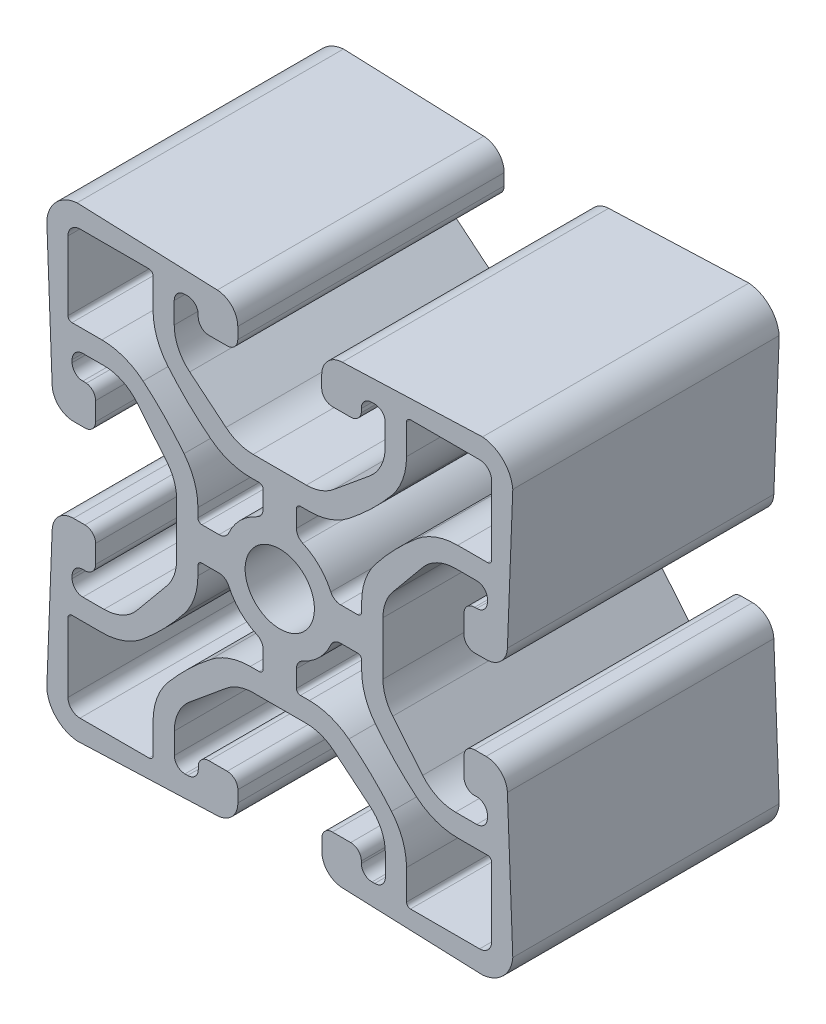
SolidWorks part; units mm, degrees
material "6061 Alloy"
ref_plane "Front" through (0, 0, 0) normal (0, 0, 1) x (1, 0, 0)
ref_plane "Top" through (0, 0, 0) normal (0, 1, 0) x (1, 0, 0)
ref_plane "Right" through (0, 0, 0) normal (1, 0, 0) x (0, 0, -1)
sketch "Sketch1" plane through (0, 0, 0) normal (0, 0, 1) x (1, 0, 0)
  line L0 (19.3255, 22.213) -> (5.9504, 21.6992)
  line L1 (22.2128, 19.328) -> (21.6992, 5.9586)
  line L2 (3.9964, 18.5751) -> (3.9964, 19.6687)
  line L3 (18.5751, 4.0046) -> (19.6687, 4.0046)
  line L4 (5.0124, 17.5591) -> (6.7625, 17.5591)
  line L5 (17.5591, 6.7605) -> (17.5591, 5.0206)
  line L6 (7.7683, 18.4316) -> (7.7683, 18.4431)
  line L7 (18.7783, 7.7765) -> (18.5751, 7.7765)
  line L8 (7.7683, 18.4431) -> (7.7683, 18.7783)
  line L9 (19.7943, 9.0465) -> (19.7943, 8.7925)
  line L10 (8.7843, 19.7943) -> (9.0383, 19.7943)
  line L11 (18.7783, 10.0625) -> (16.7556, 10.0625)
  line L12 (10.0543, 18.7783) -> (10.0543, 16.7556)
  line L13 (13.6222, 8.5866) -> (10.7682, 5.1313)
  line L14 (8.5785, 13.6222) -> (5.1232, 10.7682)
  line L15 (9.8375, 0.0041) -> (9.8375, 2.5432)
  line L16 (-0.0041, 9.8375) -> (2.5351, 9.8375)
  line L17 (9.8375, 0.0041) -> (9.8375, -2.5351)
  line L18 (-0.0041, 9.8375) -> (-2.5432, 9.8375)
  line L19 (13.6222, -8.5785) -> (10.7682, -5.1232)
  line L20 (-8.5866, 13.6222) -> (-5.1313, 10.7682)
  line L21 (18.7783, -10.0543) -> (16.7556, -10.0543)
  line L22 (-10.0625, 18.7783) -> (-10.0625, 16.7556)
  line L23 (19.7943, -8.7843) -> (19.7943, -9.0383)
  line L24 (-9.0465, 19.7943) -> (-8.7925, 19.7943)
  line L25 (18.4431, -7.7683) -> (18.7783, -7.7683)
  line L26 (-7.7765, 18.7783) -> (-7.7765, 18.5751)
  line L27 (18.4316, -7.7683) -> (18.4431, -7.7683)
  line L28 (-6.7605, 17.5591) -> (-5.0206, 17.5591)
  line L29 (17.5591, -5.0124) -> (17.5591, -6.7625)
  line L30 (-4.0046, 18.5751) -> (-4.0046, 19.6687)
  line L31 (18.5751, -3.9964) -> (19.6687, -3.9964)
  line L32 (-19.328, 22.2128) -> (-5.9586, 21.6992)
  line L33 (22.213, -19.3255) -> (21.6992, -5.9504)
  line L34 (-22.213, 19.3255) -> (-21.6992, 5.9504)
  line L35 (19.328, -22.2128) -> (5.9586, -21.6992)
  line L36 (-18.5751, 3.9964) -> (-19.6687, 3.9964)
  line L37 (4.0046, -18.5751) -> (4.0046, -19.6687)
  line L38 (-17.5591, 5.0124) -> (-17.5591, 6.7625)
  line L39 (6.7605, -17.5591) -> (5.0206, -17.5591)
  line L40 (-18.4316, 7.7683) -> (-18.4431, 7.7683)
  line L41 (7.7765, -18.7783) -> (7.7765, -18.5751)
  line L42 (-18.4431, 7.7683) -> (-18.7783, 7.7683)
  line L43 (9.0465, -19.7943) -> (8.7925, -19.7943)
  line L44 (-19.7943, 8.7843) -> (-19.7943, 9.0383)
  line L45 (10.0625, -18.7783) -> (10.0625, -16.7556)
  line L46 (-18.7783, 10.0543) -> (-16.7556, 10.0543)
  line L47 (8.5866, -13.6222) -> (5.1313, -10.7682)
  line L48 (-13.6222, 8.5785) -> (-10.7682, 5.1232)
  line L49 (0.0041, -9.8375) -> (2.5432, -9.8375)
  line L50 (-9.8375, -0.0041) -> (-9.8375, 2.5351)
  line L51 (0.0041, -9.8375) -> (-2.5351, -9.8375)
  line L52 (-9.8375, -0.0041) -> (-9.8375, -2.5432)
  line L53 (-8.5785, -13.6222) -> (-5.1232, -10.7682)
  line L54 (-13.6222, -8.5866) -> (-10.7682, -5.1313)
  line L55 (-10.0543, -18.7783) -> (-10.0543, -16.7556)
  line L56 (-18.7783, -10.0625) -> (-16.7556, -10.0625)
  line L57 (-8.7843, -19.7943) -> (-9.0383, -19.7943)
  line L58 (-19.7943, -9.0465) -> (-19.7943, -8.7925)
  line L59 (-7.7683, -18.4431) -> (-7.7683, -18.7783)
  line L60 (-18.7783, -7.7765) -> (-18.5751, -7.7765)
  line L61 (-7.7683, -18.4316) -> (-7.7683, -18.4431)
  line L62 (-17.5591, -6.7605) -> (-17.5591, -5.0206)
  line L63 (-5.0124, -17.5591) -> (-6.7625, -17.5591)
  line L64 (-18.5751, -4.0046) -> (-19.6687, -4.0046)
  line L65 (-3.9964, -18.5751) -> (-3.9964, -19.6687)
  line L66 (-22.2128, -19.328) -> (-21.6992, -5.9586)
  line L67 (-19.3255, -22.213) -> (-5.9504, -21.6992)
  line L68 (-1.5875, -7.4245) -> (-1.5875, -5.7917)
  line L69 (-1.9685, -7.8055) -> (-2.8117, -7.8055)
  line L70 (-5.7917, -1.5875) -> (-7.4245, -1.5875)
  line L71 (-12.0821, -16.9617) -> (-12.0821, -19.812)
  line L72 (-7.8055, -2.8198) -> (-7.8055, -1.9685)
  line L73 (-12.4631, -20.193) -> (-19.05, -20.193)
  line L74 (-20.193, -19.05) -> (-20.193, -12.4631)
  line L75 (-19.812, -12.0821) -> (-16.9617, -12.0821)
  line L76 (-7.4245, 1.5875) -> (-5.7917, 1.5875)
  line L77 (-7.8055, 1.9685) -> (-7.8055, 2.8117)
  line L78 (-1.5875, 5.7917) -> (-1.5875, 7.4245)
  line L79 (-16.9617, 12.0821) -> (-19.812, 12.0821)
  line L80 (-2.8198, 7.8055) -> (-1.9685, 7.8055)
  line L81 (-20.193, 12.4631) -> (-20.193, 19.05)
  line L82 (-19.05, 20.193) -> (-12.4631, 20.193)
  line L83 (-12.0821, 19.812) -> (-12.0821, 16.9617)
  line L84 (7.4245, -1.5875) -> (5.7917, -1.5875)
  line L85 (7.8055, -1.9685) -> (7.8055, -2.8117)
  line L86 (1.5875, -5.7917) -> (1.5875, -7.4245)
  line L87 (16.9617, -12.0821) -> (19.812, -12.0821)
  line L88 (2.8198, -7.8055) -> (1.9685, -7.8055)
  line L89 (20.193, -12.4631) -> (20.193, -19.05)
  line L90 (19.05, -20.193) -> (12.4631, -20.193)
  line L91 (12.0821, -19.812) -> (12.0821, -16.9617)
  line L92 (7.8055, 2.8198) -> (7.8055, 1.9685)
  line L93 (5.7917, 1.5875) -> (7.4245, 1.5875)
  line L94 (19.812, 12.0821) -> (16.9617, 12.0821)
  line L95 (1.5875, 7.4245) -> (1.5875, 5.7917)
  line L96 (20.193, 19.05) -> (20.193, 12.4631)
  line L97 (1.9685, 7.8055) -> (2.8117, 7.8055)
  line L98 (12.4631, 20.193) -> (19.05, 20.193)
  line L99 (12.0821, 16.9617) -> (12.0821, 19.812)
  circle A0 centre (0, 0) radius 3.302
  arc A1 (22.2128, 19.328) -> (19.3255, 22.213) centre (19.05, 19.05) ccw
  arc A2 (5.9504, 21.6992) -> (3.9964, 19.6687) centre (6.0284, 19.6687) ccw
  arc A3 (19.6687, 4.0046) -> (21.6992, 5.9586) centre (19.6687, 6.0366) ccw
  arc A4 (3.9964, 18.5751) -> (5.0124, 17.5591) centre (5.0124, 18.5751) ccw
  arc A5 (17.5591, 5.0206) -> (18.5751, 4.0046) centre (18.5751, 5.0206) ccw
  arc A6 (6.7625, 17.5591) -> (7.7683, 18.4316) centre (6.7625, 18.5751) ccw
  arc A7 (18.5751, 7.7765) -> (17.5591, 6.7605) centre (18.5751, 6.7605) ccw
  arc A8 (18.7783, 7.7765) -> (19.7943, 8.7925) centre (18.7783, 8.7925) ccw
  arc A9 (8.7843, 19.7943) -> (7.7683, 18.7783) centre (8.7843, 18.7783) ccw
  arc A10 (19.7943, 9.0465) -> (18.7783, 10.0625) centre (18.7783, 9.0465) ccw
  arc A11 (10.0543, 18.7783) -> (9.0383, 19.7943) centre (9.0383, 18.7783) ccw
  arc A12 (16.7556, 10.0625) -> (13.6222, 8.5866) centre (16.7556, 5.9985) ccw
  arc A13 (8.5785, 13.6222) -> (10.0543, 16.7556) centre (5.9903, 16.7556) ccw
  arc A14 (10.7682, 5.1313) -> (9.8375, 2.5432) centre (13.9015, 2.5432) ccw
  arc A15 (2.5351, 9.8375) -> (5.1232, 10.7682) centre (2.5351, 13.9015) ccw
  arc A16 (9.8375, -2.5351) -> (10.7682, -5.1232) centre (13.9015, -2.5351) ccw
  arc A17 (-5.1313, 10.7682) -> (-2.5432, 9.8375) centre (-2.5432, 13.9015) ccw
  arc A18 (13.6222, -8.5785) -> (16.7556, -10.0543) centre (16.7556, -5.9903) ccw
  arc A19 (-10.0625, 16.7556) -> (-8.5866, 13.6222) centre (-5.9985, 16.7556) ccw
  arc A20 (18.7783, -10.0543) -> (19.7943, -9.0383) centre (18.7783, -9.0383) ccw
  arc A21 (-9.0465, 19.7943) -> (-10.0625, 18.7783) centre (-9.0465, 18.7783) ccw
  arc A22 (19.7943, -8.7843) -> (18.7783, -7.7683) centre (18.7783, -8.7843) ccw
  arc A23 (-7.7765, 18.7783) -> (-8.7925, 19.7943) centre (-8.7925, 18.7783) ccw
  arc A24 (-7.7765, 18.5751) -> (-6.7605, 17.5591) centre (-6.7605, 18.5751) ccw
  arc A25 (17.5591, -6.7625) -> (18.4316, -7.7683) centre (18.5751, -6.7625) ccw
  arc A26 (-5.0206, 17.5591) -> (-4.0046, 18.5751) centre (-5.0206, 18.5751) ccw
  arc A27 (18.5751, -3.9964) -> (17.5591, -5.0124) centre (18.5751, -5.0124) ccw
  arc A28 (-4.0046, 19.6687) -> (-5.9586, 21.6992) centre (-6.0366, 19.6687) ccw
  arc A29 (21.6992, -5.9504) -> (19.6687, -3.9964) centre (19.6687, -6.0284) ccw
  arc A30 (-19.328, 22.2128) -> (-22.213, 19.3255) centre (-19.05, 19.05) ccw
  arc A31 (19.328, -22.2128) -> (22.213, -19.3255) centre (19.05, -19.05) ccw
  arc A32 (-21.6992, 5.9504) -> (-19.6687, 3.9964) centre (-19.6687, 6.0284) ccw
  arc A33 (4.0046, -19.6687) -> (5.9586, -21.6992) centre (6.0366, -19.6687) ccw
  arc A34 (-18.5751, 3.9964) -> (-17.5591, 5.0124) centre (-18.5751, 5.0124) ccw
  arc A35 (5.0206, -17.5591) -> (4.0046, -18.5751) centre (5.0206, -18.5751) ccw
  arc A36 (-17.5591, 6.7625) -> (-18.4316, 7.7683) centre (-18.5751, 6.7625) ccw
  arc A37 (7.7765, -18.5751) -> (6.7605, -17.5591) centre (6.7605, -18.5751) ccw
  arc A38 (7.7765, -18.7783) -> (8.7925, -19.7943) centre (8.7925, -18.7783) ccw
  arc A39 (-19.7943, 8.7843) -> (-18.7783, 7.7683) centre (-18.7783, 8.7843) ccw
  arc A40 (9.0465, -19.7943) -> (10.0625, -18.7783) centre (9.0465, -18.7783) ccw
  arc A41 (-18.7783, 10.0543) -> (-19.7943, 9.0383) centre (-18.7783, 9.0383) ccw
  arc A42 (10.0625, -16.7556) -> (8.5866, -13.6222) centre (5.9985, -16.7556) ccw
  arc A43 (-13.6222, 8.5785) -> (-16.7556, 10.0543) centre (-16.7556, 5.9903) ccw
  arc A44 (5.1313, -10.7682) -> (2.5432, -9.8375) centre (2.5432, -13.9015) ccw
  arc A45 (-9.8375, 2.5351) -> (-10.7682, 5.1232) centre (-13.9015, 2.5351) ccw
  arc A46 (-2.5351, -9.8375) -> (-5.1232, -10.7682) centre (-2.5351, -13.9015) ccw
  arc A47 (-10.7682, -5.1313) -> (-9.8375, -2.5432) centre (-13.9015, -2.5432) ccw
  arc A48 (-8.5785, -13.6222) -> (-10.0543, -16.7556) centre (-5.9903, -16.7556) ccw
  arc A49 (-16.7556, -10.0625) -> (-13.6222, -8.5866) centre (-16.7556, -5.9985) ccw
  arc A50 (-10.0543, -18.7783) -> (-9.0383, -19.7943) centre (-9.0383, -18.7783) ccw
  arc A51 (-19.7943, -9.0465) -> (-18.7783, -10.0625) centre (-18.7783, -9.0465) ccw
  arc A52 (-8.7843, -19.7943) -> (-7.7683, -18.7783) centre (-8.7843, -18.7783) ccw
  arc A53 (-18.7783, -7.7765) -> (-19.7943, -8.7925) centre (-18.7783, -8.7925) ccw
  arc A54 (-18.5751, -7.7765) -> (-17.5591, -6.7605) centre (-18.5751, -6.7605) ccw
  arc A55 (-6.7625, -17.5591) -> (-7.7683, -18.4316) centre (-6.7625, -18.5751) ccw
  arc A56 (-17.5591, -5.0206) -> (-18.5751, -4.0046) centre (-18.5751, -5.0206) ccw
  arc A57 (-3.9964, -18.5751) -> (-5.0124, -17.5591) centre (-5.0124, -18.5751) ccw
  arc A58 (-19.6687, -4.0046) -> (-21.6992, -5.9586) centre (-19.6687, -6.0366) ccw
  arc A59 (-5.9504, -21.6992) -> (-3.9964, -19.6687) centre (-6.0284, -19.6687) ccw
  arc A60 (-22.2128, -19.328) -> (-19.3255, -22.213) centre (-19.05, -19.05) ccw
  arc A61 (-1.9685, -7.8055) -> (-1.5875, -7.4245) centre (-1.9685, -7.4245) ccw
  arc A62 (-1.5875, -5.7917) -> (-2.1869, -4.8651) centre (-2.6035, -5.7917) ccw
  arc A63 (-2.8117, -7.8055) -> (-6.6038, -9.1286) centre (-2.8117, -13.9015) ccw
  arc A64 (-4.8651, -2.1869) -> (-2.1869, -4.8651) centre (0, 0) ccw
  arc A65 (-6.6038, -9.1286) -> (-10.6477, -13.0335) centre (10.3295, -30.7105) ccw
  arc A66 (-4.8651, -2.1869) -> (-5.7917, -1.5875) centre (-5.7917, -2.6035) ccw
  arc A67 (-10.6477, -13.0335) -> (-12.0821, -16.9617) centre (-5.9861, -16.9617) ccw
  arc A68 (-7.4245, -1.5875) -> (-7.8055, -1.9685) centre (-7.4245, -1.9685) ccw
  arc A69 (-12.4631, -20.193) -> (-12.0821, -19.812) centre (-12.4631, -19.812) ccw
  arc A70 (-9.1044, -6.5813) -> (-7.8055, -2.8198) centre (-13.9015, -2.8198) ccw
  arc A71 (-20.193, -19.05) -> (-19.05, -20.193) centre (-19.05, -19.05) ccw
  arc A72 (-13.039, -10.6523) -> (-9.1044, -6.5813) centre (-30.6913, 10.3456) ccw
  arc A73 (-16.9617, -12.0821) -> (-13.039, -10.6523) centre (-16.9617, -5.9861) ccw
  arc A74 (-19.812, -12.0821) -> (-20.193, -12.4631) centre (-19.812, -12.4631) ccw
  arc A75 (-7.8055, 1.9685) -> (-7.4245, 1.5875) centre (-7.4245, 1.9685) ccw
  arc A76 (-5.7917, 1.5875) -> (-4.8651, 2.1869) centre (-5.7917, 2.6035) ccw
  arc A77 (-7.8055, 2.8117) -> (-9.1286, 6.6038) centre (-13.9015, 2.8117) ccw
  arc A78 (-2.1869, 4.8651) -> (-4.8651, 2.1869) centre (0, 0) ccw
  arc A79 (-9.1286, 6.6038) -> (-13.0335, 10.6477) centre (-30.7105, -10.3295) ccw
  arc A80 (-2.1869, 4.8651) -> (-1.5875, 5.7917) centre (-2.6035, 5.7917) ccw
  arc A81 (-13.0335, 10.6477) -> (-16.9617, 12.0821) centre (-16.9617, 5.9861) ccw
  arc A82 (-1.5875, 7.4245) -> (-1.9685, 7.8055) centre (-1.9685, 7.4245) ccw
  arc A83 (-20.193, 12.4631) -> (-19.812, 12.0821) centre (-19.812, 12.4631) ccw
  arc A84 (-6.5813, 9.1044) -> (-2.8198, 7.8055) centre (-2.8198, 13.9015) ccw
  arc A85 (-19.05, 20.193) -> (-20.193, 19.05) centre (-19.05, 19.05) ccw
  arc A86 (-10.6523, 13.039) -> (-6.5813, 9.1044) centre (10.3456, 30.6913) ccw
  arc A87 (-12.0821, 16.9617) -> (-10.6523, 13.039) centre (-5.9861, 16.9617) ccw
  arc A88 (-12.0821, 19.812) -> (-12.4631, 20.193) centre (-12.4631, 19.812) ccw
  arc A89 (7.8055, -1.9685) -> (7.4245, -1.5875) centre (7.4245, -1.9685) ccw
  arc A90 (5.7917, -1.5875) -> (4.8651, -2.1869) centre (5.7917, -2.6035) ccw
  arc A91 (7.8055, -2.8117) -> (9.1286, -6.6038) centre (13.9015, -2.8117) ccw
  arc A92 (2.1869, -4.8651) -> (4.8651, -2.1869) centre (0, 0) ccw
  arc A93 (9.1286, -6.6038) -> (13.0335, -10.6477) centre (30.7105, 10.3295) ccw
  arc A94 (2.1869, -4.8651) -> (1.5875, -5.7917) centre (2.6035, -5.7917) ccw
  arc A95 (13.0335, -10.6477) -> (16.9617, -12.0821) centre (16.9617, -5.9861) ccw
  arc A96 (1.5875, -7.4245) -> (1.9685, -7.8055) centre (1.9685, -7.4245) ccw
  arc A97 (20.193, -12.4631) -> (19.812, -12.0821) centre (19.812, -12.4631) ccw
  arc A98 (6.5813, -9.1044) -> (2.8198, -7.8055) centre (2.8198, -13.9015) ccw
  arc A99 (19.05, -20.193) -> (20.193, -19.05) centre (19.05, -19.05) ccw
  arc A100 (10.6523, -13.039) -> (6.5813, -9.1044) centre (-10.3456, -30.6913) ccw
  arc A101 (12.0821, -16.9617) -> (10.6523, -13.039) centre (5.9861, -16.9617) ccw
  arc A102 (12.0821, -19.812) -> (12.4631, -20.193) centre (12.4631, -19.812) ccw
  arc A103 (7.4245, 1.5875) -> (7.8055, 1.9685) centre (7.4245, 1.9685) ccw
  arc A104 (9.1044, 6.5813) -> (7.8055, 2.8198) centre (13.9015, 2.8198) ccw
  arc A105 (4.8651, 2.1869) -> (5.7917, 1.5875) centre (5.7917, 2.6035) ccw
  arc A106 (13.039, 10.6523) -> (9.1044, 6.5813) centre (30.6913, -10.3456) ccw
  arc A107 (4.8651, 2.1869) -> (2.1869, 4.8651) centre (0, 0) ccw
  arc A108 (16.9617, 12.0821) -> (13.039, 10.6523) centre (16.9617, 5.9861) ccw
  arc A109 (1.5875, 5.7917) -> (2.1869, 4.8651) centre (2.6035, 5.7917) ccw
  arc A110 (19.812, 12.0821) -> (20.193, 12.4631) centre (19.812, 12.4631) ccw
  arc A111 (1.9685, 7.8055) -> (1.5875, 7.4245) centre (1.9685, 7.4245) ccw
  arc A112 (20.193, 19.05) -> (19.05, 20.193) centre (19.05, 19.05) ccw
  arc A113 (2.8117, 7.8055) -> (6.6038, 9.1286) centre (2.8117, 13.9015) ccw
  arc A114 (6.6038, 9.1286) -> (10.6477, 13.0335) centre (-10.3295, 30.7105) ccw
  arc A115 (12.4631, 20.193) -> (12.0821, 19.812) centre (12.4631, 19.812) ccw
  arc A116 (10.6477, 13.0335) -> (12.0821, 16.9617) centre (5.9861, 16.9617) ccw
extrude "Extrude1" add sketch "Sketch1" along normal blind 25.4
